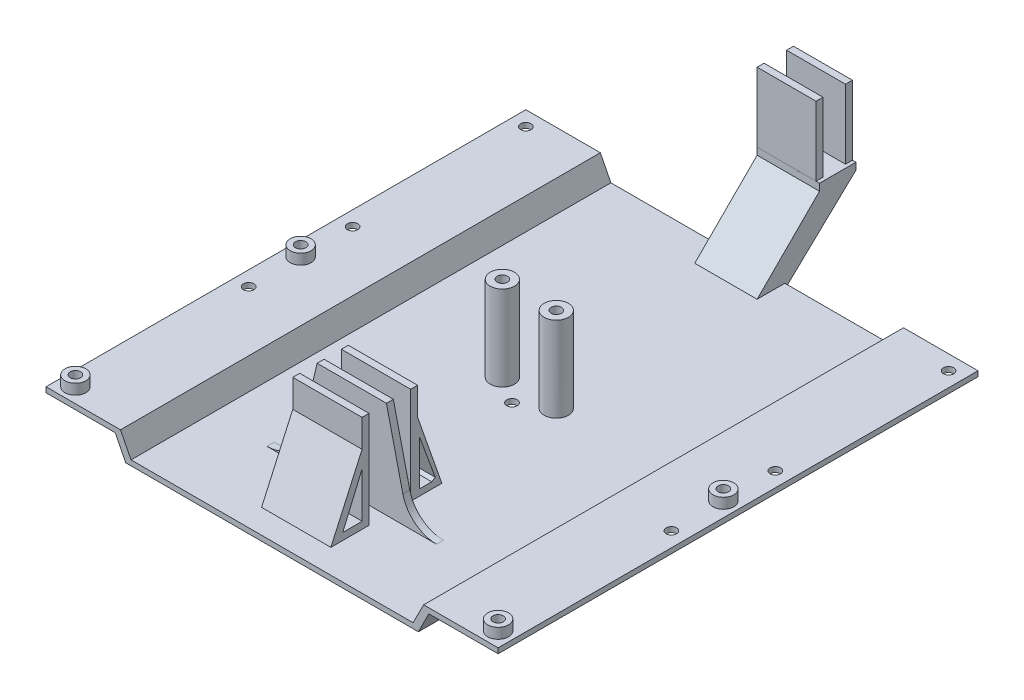
SolidWorks part; units mm, degrees
ref_plane "Front Plane" through (0, 0, 0) normal (0, 0, 1) x (1, 0, 0)
ref_plane "Top Plane" through (0, 0, 0) normal (0, 1, 0) x (1, 0, 0)
ref_plane "Right Plane" through (0, 0, 0) normal (1, 0, 0) x (0, 0, -1)
sketch "Sketch1" plane through (0, 0, 0) normal (0, 1, 0) x (1, 0, 0)
  line L0 (0, 0) -> (122, 0) construction
  line L1 (0, 0) -> (0, -130) construction
  line L2 (0, -130) -> (122, -130) construction
  line L3 (0, 0) -> (-4.2426, 4.2426) construction
  line L4 (122, -130) -> (126.2426, -134.2426) construction
  line L6 (-4.2426, 4.2426) -> (126.2426, 4.2426)
  line L7 (-4.2426, 4.2426) -> (-4.2426, -134.2426)
  line L8 (-4.2426, -134.2426) -> (126.2426, -134.2426)
  line L9 (126.2426, 4.2426) -> (126.2426, -134.2426)
  circle A0 centre (0, 0) radius 1.5
  circle A1 centre (122, 0) radius 1.5
  circle A2 centre (0, -130) radius 1.5
  circle A3 centre (122, -130) radius 1.5
  dimension "D1" = 122
  dimension "D2" = 130
  dimension "D3" = 6
extrude "Boss-Extrude1" add sketch "Sketch1" along normal blind 1.5 contours A3 | A2 | A0 | A1 | L7 L6 L9 L8
sketch "Sketch3" plane through (0, 1.5, 0) normal (0, 1, 0) x (1, 0, 0)
  line L0 (-4.2426, -65) -> (15.7574, -65) construction
  line L1 (-4.2426, 4.2426) -> (-4.2426, -134.2426) construction
  line L2 (15.7574, -65) -> (15.7574, 4.2426)
  line L3 (-4.2426, 4.2426) -> (126.2426, 4.2426) construction
  line L4 (15.7574, -65) -> (15.7574, -134.2426)
  line L5 (-4.2426, -134.2426) -> (126.2426, -134.2426) construction
  line L6 (61, 4.2426) -> (61, -62.9629) construction
  line L7 (106.2426, -65) -> (106.2426, -134.2426)
  line L8 (106.2426, -65) -> (106.2426, 4.2426)
  line L9 (15.7574, 4.2426) -> (106.2426, 4.2426)
  line L10 (106.2426, -134.2426) -> (15.7574, -134.2426)
  dimension "D1" = 20
extrude "Cut-Extrude1" cut sketch "Sketch3" against normal blind 17.5
sketch "Sketch4" plane through (0, 0, 134.2426) normal (0, 0, 1) x (1, 0, 0)
  line L0 (15.7574, 0) -> (15.7574, -6) construction
  line L1 (15.7574, -6) -> (18.7574, -6) construction
  line L2 (15.7574, 0) -> (18.7574, -6)
  line L3 (15.7574, 0.75) -> (106.2426, 0.75) construction
  line L4 (15.7574, 0) -> (15.7574, 1.5) construction
  line L5 (106.2426, 0) -> (106.2426, 1.5) construction
  line L6 (61, 0.75) -> (61, -2.6317) construction
  line L7 (18.7574, -6) -> (103.2426, -6)
  line L8 (15.7574, 1.5) -> (17.2574, 1.5)
  line L9 (31.5588, -6) -> (31.5588, -4.5) construction
  line L10 (17.2574, 1.5) -> (20.2961, -4.5)
  line L11 (20.2961, -4.5) -> (38.3727, -4.5)
  line L12 (38.3727, -4.5) -> (83.6273, -4.5)
  line L13 (104.7426, 1.5) -> (101.7039, -4.5)
  line L14 (106.2426, 0) -> (103.2426, -6)
  line L15 (106.2426, 1.5) -> (104.7426, 1.5)
  line L16 (101.7039, -4.5) -> (83.6273, -4.5)
  line L17 (15.7574, 1.5) -> (15.7574, 0)
  line L18 (106.2426, 1.5) -> (106.2426, 0)
  point P18 (61, -6)
  point P27 (61, -4.5)
  dimension "D1" = 6
  dimension "D2" = 3
  dimension "D3" = 1.5
  dimension "D4" = 1.5
extrude "Boss-Extrude2" add sketch "Sketch4" against normal through all
sketch "Sketch14" plane through (0, 1.5, 0) normal (0, 1, 0) x (1, 0, 0)
  line L0 (61, -134.2426) -> (61, -121.7294) construction
  line L1 (101.7039, -134.2426) -> (20.2961, -134.2426) construction
  circle A0 centre (0, -130) radius 1.5
  circle A1 centre (0, -130) radius 3
  circle A2 centre (122, -130) radius 1.5
  circle A3 centre (122, -130) radius 3
extrude "Boss-Extrude7" add sketch "Sketch14" along normal blind 3
sketch "Sketch15" plane through (0, 1.5, 0) normal (0, 1, 0) x (1, 0, 0)
  line L0 (0, -130) -> (0, -65) construction
  line L1 (61, -134.2426) -> (61, -125.9107) construction
  line L2 (101.7039, -134.2426) -> (20.2961, -134.2426) construction
  circle A0 centre (0, -65) radius 1.5
  circle A1 centre (122, -65) radius 1.5
  dimension "D1" = 65
extrude "Cut-Extrude6" cut sketch "Sketch15" against normal blind 3
sketch "Sketch16" plane through (0, 1.5, 0) normal (0, 1, 0) x (1, 0, 0)
  line L0 (61, -134.2426) -> (61, -121.7051) construction
  line L1 (101.7039, -134.2426) -> (20.2961, -134.2426) construction
  circle A0 centre (0, -65) radius 3
  circle A1 centre (122, -65) radius 3
  circle A2 centre (0, -65) radius 1.5
  circle A3 centre (122, -65) radius 1.5
extrude "Boss-Extrude8" add sketch "Sketch16" along normal blind 3
sketch "Sketch17" plane through (0, 1.5, 0) normal (0, 1, 0) x (1, 0, 0)
  line L0 (0, -65) -> (0, -50) construction
  line L1 (0, -65) -> (6.6664, -65) construction
  line L2 (61, -134.2426) -> (61, -121.4665) construction
  line L3 (101.7039, -134.2426) -> (20.2961, -134.2426) construction
  circle A0 centre (0, -50) radius 1.5
  circle A1 centre (0, -80) radius 1.5
  circle A2 centre (122, -80) radius 1.5
  circle A3 centre (122, -50) radius 1.5
  dimension "D1" = 15
extrude "Cut-Extrude7" cut sketch "Sketch17" against normal blind 3
sketch "Sketch18" plane through (0, -4.5, 0) normal (0, 1, 0) x (1, 0, 0)
  line L0 (61, 4.2426) -> (61, -134.2426) construction
  line L1 (101.7039, 4.2426) -> (20.2961, 4.2426) construction
  line L2 (101.7039, -134.2426) -> (20.2961, -134.2426) construction
  line L3 (61, -65) -> (53.22, -65) construction
  line L4 (53.22, -65) -> (53.22, -60) construction
  circle A0 centre (53.22, -60) radius 1.5
  circle A1 centre (53.22, -60) radius 3.5
  circle A2 centre (68.78, -60) radius 3.5
  circle A3 centre (68.78, -60) radius 1.5
  dimension "D1" = 7.78
  dimension "D2" = 5
extrude "Boss-Extrude9" add sketch "Sketch18" along normal blind 24.5 contours A1 | A2 | A0 | A3
sketch "Sketch19" plane through (0, -4.5, 0) normal (0, 1, 0) x (1, 0, 0)
  line L0 (61, -134.2426) -> (61, -109.2426) construction
  line L1 (101.7039, -134.2426) -> (20.2961, -134.2426) construction
  line L2 (61, -109.2426) -> (51, -109.2426) construction
  line L3 (61, -109.2426) -> (71, -109.2426) construction
  line L4 (51, -109.2426) -> (51, -111.2426) construction
  line L5 (61, -109.2426) -> (61, -104.2426) construction
  line L6 (51, -111.2426) -> (71, -111.2426)
  line L7 (51, -111.2426) -> (51, -109.2426)
  line L8 (51, -109.2426) -> (71, -109.2426)
  line L9 (71, -111.2426) -> (71, -109.2426)
  line L10 (51, -104.2426) -> (61, -104.2426) construction
  line L11 (61, -104.2426) -> (71, -104.2426) construction
  line L12 (71, -104.2426) -> (71, -102.2426) construction
  line L14 (51, -104.2426) -> (71, -104.2426)
  line L15 (51, -104.2426) -> (51, -102.2426)
  line L16 (51, -102.2426) -> (71, -102.2426)
  line L17 (71, -104.2426) -> (71, -102.2426)
  dimension "D1" = 25
  dimension "D2" = 10
  dimension "D3" = 10
  dimension "D4" = 2
  dimension "D5" = 5
  dimension "D6" = 2
extrude "Boss-Extrude10" add sketch "Sketch19" along normal blind 28 contours L6 L9 L8 L7 | L15 L14 L17 L16
sketch "Sketch20" plane through (71, 0, 0) normal (1, 0, 0) x (0, 0, -1)
  line L0 (-111.2426, -4.5) -> (-111.2426, 15.5) construction
  line L1 (-111.2426, 23.5) -> (-111.2426, -4.5) construction
  line L2 (-111.2426, -4.5) -> (-118.2426, -4.5)
  line L3 (-118.2426, -4.5) -> (-111.2426, 15.5)
  line L4 (-111.2426, 15.5) -> (-111.2426, -4.5)
  line L5 (-109.2426, -4.5) -> (-104.2426, -4.5) construction
  line L6 (-106.7426, -4.5) -> (-106.7426, 0) construction
  line L7 (-115.3294, -2.6686) -> (-111.8038, -2.6686)
  line L8 (-111.8038, -2.6686) -> (-111.8038, 10.2973)
  line L9 (-111.8038, 10.2973) -> (-116.3374, -2.0408)
  line L10 (-116.3374, -2.0408) -> (-115.3294, -2.6686)
  line L11 (-101.6815, 10.2973) -> (-97.1479, -2.0408)
  line L12 (-101.6815, -2.6686) -> (-101.6815, 10.2973)
  line L13 (-98.1559, -2.6686) -> (-101.6815, -2.6686)
  line L14 (-97.1479, -2.0408) -> (-98.1559, -2.6686)
  line L15 (-95.2426, -4.5) -> (-102.2426, 15.5)
  line L16 (-102.2426, -4.5) -> (-95.2426, -4.5)
  line L17 (-102.2426, 15.5) -> (-102.2426, -4.5)
  dimension "D1" = 20
  dimension "D2" = 7
extrude "Boss-Extrude11" add sketch "Sketch20" against normal blind 20
sketch "Sketch24" plane through (0, -4.5, 0) normal (0, 1, 0) x (1, 0, 0)
  line L0 (61, 4.2426) -> (61, -134.2426) construction
  line L1 (101.7039, 4.2426) -> (20.2961, 4.2426) construction
  line L2 (101.7039, -134.2426) -> (20.2961, -134.2426) construction
  circle A0 centre (61, -65) radius 1.5
extrude "Cut-Extrude9" cut sketch "Sketch24" against normal blind 16
sketch "Sketch27" plane through (0, -4.5, 0) normal (0, 1, 0) x (1, 0, 0)
  line L0 (61, 4.2426) -> (61, 14.2426) construction
  line L1 (101.7039, 4.2426) -> (20.2961, 4.2426) construction
  line L2 (61, 14.2426) -> (52.5, 14.2426)
  line L3 (52.5, 14.2426) -> (52.5, 16.2426)
  line L4 (61, 14.2426) -> (69.5, 14.2426) construction
  line L5 (61, 16.2426) -> (61, 22.7426) construction
  line L6 (52.5, 16.2426) -> (69.5, 16.2426)
  line L7 (52.5, 16.2426) -> (52.5, 14.2426)
  line L8 (52.5, 14.2426) -> (69.5, 14.2426)
  line L9 (69.5, 16.2426) -> (69.5, 14.2426)
  line L10 (61, 22.7426) -> (52.5, 22.7426) construction
  line L11 (69.5, 14.2426) -> (69.5, 7.1661) construction
  line L12 (69.5, 7.1661) -> (69.5, 5.1661) construction
  line L18 (52.5, 22.7426) -> (69.5, 22.7426)
  line L19 (52.5, 22.7426) -> (52.5, 24.7426)
  line L20 (52.5, 24.7426) -> (69.5, 24.7426)
  line L21 (69.5, 22.7426) -> (69.5, 24.7426)
  dimension "D1" = 10
  dimension "D2" = 8.5
  dimension "D3" = 2
  dimension "D4" = 8.5
  dimension "D5" = 6.5
  dimension "D6" = 2
  dimension "D7" = 2
extrude "Boss-Extrude13" add sketch "Sketch27" along normal blind 40 separate body contours L9 L6 L3 L2 L8 | L19 L18 L21 L20
sketch "Sketch28" plane through (0, -4.5, 0) normal (0, -1, 0) x (1, 0, 0)
  line L1 (46.1941, -10.7411) -> (75.7306, -10.7411)
  line L2 (46.1941, -10.7411) -> (46.1941, -26.5844)
  line L3 (46.1941, -26.5844) -> (75.7306, -26.5844)
  line L4 (75.7306, -10.7411) -> (75.7306, -26.5844)
extrude "Cut-Extrude10" cut sketch "Sketch28" against normal blind 20
sketch "Sketch29" plane through (52.5, 0, 0) normal (-1, 0, 0) x (0, 0, 1)
  line L0 (-24.7426, 13.5) -> (-4.2426, -6)
  line L1 (-24.7426, 15.5) -> (-14.2417, 15.5)
  line L2 (-24.7426, 15.5) -> (-24.7426, 13.5)
  line L4 (-14.2417, 15.5) -> (-14.2417, 13.5)
  line L5 (-14.2417, 13.5) -> (4.7384, -5.4801)
  line L6 (4.7384, -5.4801) -> (-4.2426, -6)
  dimension "D1" = 2
extrude "Boss-Extrude14" add sketch "Sketch29" against normal blind 18
sketch "Sketch30" plane through (51, 0, 0) normal (-1, 0, 0) x (0, 0, 1)
  line L0 (111.2426, 15.5) -> (111.2426, -4.5)
  line L1 (118.2426, -4.5) -> (109.2426, -4.5) construction
  line L2 (111.2426, -4.5) -> (118.2426, -4.5)
  line L3 (118.2426, -4.5) -> (111.2426, 15.5)
extrude "Cut-Extrude11" cut sketch "Sketch30" against normal blind 26
sketch "Sketch32" plane through (0, 0, 111.2426) normal (0, 0, 1) x (1, 0, 0)
  line L0 (51, 23.5) -> (44.4549, -4.5)
  line L1 (101.7039, -4.5) -> (20.2961, -4.5) construction
  line L2 (44.4549, -4.5) -> (51, -4.5)
  line L3 (51, -4.5) -> (51, 23.5)
  line L4 (61, 23.5) -> (61, 15.8736) construction
  line L5 (51, 23.5) -> (71, 23.5) construction
  line L6 (77.5451, -4.5) -> (71, -4.5)
  line L7 (71, 23.5) -> (77.5451, -4.5)
  line L8 (71, -4.5) -> (71, 23.5)
  line M7 (71, -4.5) -> (71, 23.5)
extrude "Boss-Extrude15" add sketch "Sketch32" against normal blind 2 contours L7 L6 M7 | L3 L0 L2
fillet "Fillet1" radius 10 2 edges at (77.5451, -4.5, 110.2426) (44.4549, -4.5, 110.2426)
sketch "Sketch33" plane through (0, -4.5, 0) normal (0, 1, 0) x (1, 0, 0)
  line L0 (61, -111.2426) -> (61, -116.2426) construction
  line L1 (51, -111.2426) -> (71, -111.2426) construction
  line L2 (51, -111.2426) -> (51, -121.301) construction
  line L3 (71, -111.2426) -> (71, -121.301) construction
  line L4 (51, -116.2718) -> (71, -116.2718)
  line L5 (51, -116.2718) -> (51, -118.2718)
  line L6 (51, -118.2718) -> (71, -118.2718)
  line L7 (71, -118.2718) -> (71, -116.2718)
  dimension "D1" = 5
  dimension "D2" = 2
extrude "Boss-Extrude16" add sketch "Sketch33" along normal blind 28 contours L7 L4 L5 L6
sketch "Sketch34" plane through (71, 0, 0) normal (1, 0, 0) x (0, 0, -1)
  line L0 (-102.2426, 15.5) -> (-118.2718, 15.5) construction
  line L1 (-118.2718, 23.5) -> (-118.2718, -4.5) construction
  line L2 (-118.2718, -4.5) -> (-118.2718, 15.5)
  line L4 (-118.2718, -4.5) -> (-127.2718, -4.5)
  line L5 (-127.2718, -4.5) -> (-118.2718, 15.5)
  dimension "D1" = 9
extrude "Boss-Extrude17" add sketch "Sketch34" against normal blind 20 contours L5 L2 L4
sketch "Sketch35" plane through (71, 0, 0) normal (1, 0, 0) x (0, 0, -1)
  line L0 (-121.7718, -4.5) -> (-121.7718, -2.5) construction
  line L1 (-127.2718, -4.5) -> (-116.2718, -4.5) construction
  line L2 (-121.7718, -2.5) -> (-118.2365, -2.5)
  line L3 (-118.2365, -2.5) -> (-118.2365, 10.6896)
  line L4 (-118.2365, 10.6896) -> (-123.8404, -2.5)
  line L5 (-123.8404, -2.5) -> (-121.7718, -2.5)
  dimension "D1" = 2
extrude "Cut-Extrude12" cut sketch "Sketch35" against normal blind 20
